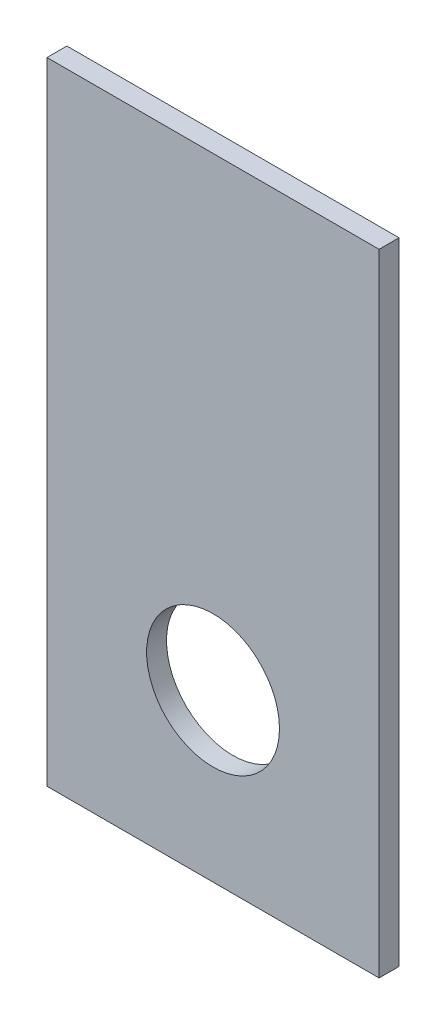
SolidWorks part; units mm, degrees
material "Cast Alloy Steel"
ref_plane "Front Plane" through (0, 0, 0) normal (0, 0, 1) x (1, 0, 0)
ref_plane "Top Plane" through (0, 0, 0) normal (0, 1, 0) x (1, 0, 0)
ref_plane "Right Plane" through (0, 0, 0) normal (1, 0, 0) x (0, 0, -1)
sketch "Sketch1" plane through (0, 0, 0) normal (0, 0, 1) x (1, 0, 0)
  line L0 (-25, 95) -> (25, 95)
  line L1 (-25, 0) -> (25, 0)
  line L2 (-25, 95) -> (-25, 0)
  line L3 (25, 95) -> (25, 0)
  circle A0 centre (0, 25) radius 10
  point P6 (0, 0)
  dimension "D5" = 20
  dimension "D6" = 25
  dimension "D7" = 25
  dimension "D1" = 50
  dimension "D2" = 95
  dimension "D3" = 25
  dimension "D4" = 50
extrude "Boss-Extrude1" add sketch "Sketch1" along normal blind 3
